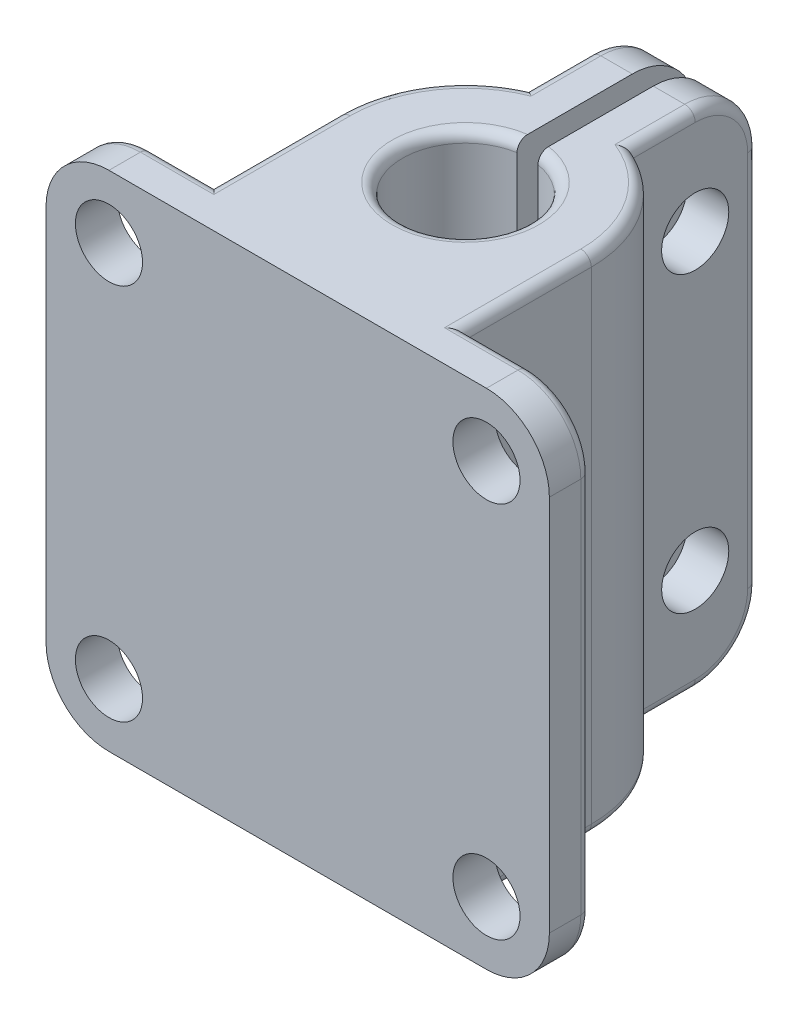
SolidWorks part; units mm, degrees
ref_plane "Front Plane" through (0, 0, 0) normal (0, 0, 1) x (1, 0, 0)
ref_plane "Top Plane" through (0, 0, 0) normal (0, 1, 0) x (1, 0, 0)
ref_plane "Right Plane" through (0, 0, 0) normal (1, 0, 0) x (0, 0, -1)
sketch "Sketch1" plane through (0, 0, 0) normal (0, 1, 0) x (1, 0, 0)
  line L21 (-6, 6) -> (-6, 0)
  line L22 (-6, 0) -> (6, 0)
  line L23 (0, -6.3325) -> (0, 25.8956) construction
  line L24 (-2.5, 11.4544) -> (-2.5, 17.4544)
  line L25 (-2.5, 17.4544) -> (-0.5, 17.4544)
  line L26 (-0.5, 17.4544) -> (-0.5, 8.958)
  line L27 (6, 6) -> (6, 0)
  line L28 (2.5, 11.4544) -> (2.5, 17.4544)
  line L29 (2.5, 17.4544) -> (0.5, 17.4544)
  line L30 (0.5, 17.4544) -> (0.5, 8.958)
  circle A4 centre (0, 6) radius 3 construction
  circle A5 centre (0, 6) radius 6 construction
  arc A6 (-6, 6) -> (-2.5, 11.4544) centre (0, 6) cw
  arc A7 (-0.5, 8.958) -> (0.5, 8.958) centre (0, 6) ccw
  arc A8 (6, 6) -> (2.5, 11.4544) centre (0, 6) ccw
  point P13 (0, 0)
  dimension "D2" = 12
  dimension "D1" = 6
  dimension "D3" = 2
  dimension "D4" = 0.5
  dimension "D5" = 6
extrude "Boss-Extrude1" add sketch "Sketch1" along normal blind 24
sketch "Sketch2" plane through (2.5, 0, 0) normal (1, 0, 0) x (0, 0, -1)
  line L0 (11.4544, 24) -> (17.4544, 24) construction
  line L1 (17.4544, 12) -> (0, 12) construction
  line L3 (17.4544, 24) -> (17.4544, 0) construction
  line L4 (0, 24) -> (0, 0) construction
  circle A0 centre (14.4544, 19) radius 1.6
  circle A1 centre (14.4544, 5) radius 1.6
  point P5 (14.4544, 24)
  dimension "D2" = 3.2
  dimension "D1" = 5
extrude "Cut-Extrude1" cut sketch "Sketch2" against normal through all
sketch "Sketch3" plane through (0, 0, 0) normal (0, 0, 1) x (1, 0, 0)
  line L0 (-6, 24) -> (6, 24) construction
  line L1 (12, 0) -> (-12, 0)
  line L2 (12, 0) -> (12, 24)
  line L3 (12, 24) -> (-12, 24)
  line L4 (-12, 0) -> (-12, 24)
  line L5 (-6, 0) -> (6, 0) construction
  line L6 (6, 24) -> (6, 0) construction
  point P8 (0, 24)
  dimension "D1" = 6
extrude "Boss-Extrude2" add sketch "Sketch3" along normal blind 2
sketch "Sketch4" plane through (0, 0, 0) normal (0, 0, -1) x (-1, 0, 0)
  line L0 (12, 12) -> (-12, 12) construction
  line L1 (12, 24) -> (12, 0) construction
  line L2 (-12, 0) -> (-12, 24) construction
  line L3 (12, 0) -> (6, 0) construction
  line L4 (0, 0) -> (0, 24) construction
  line L5 (3, 24) -> (-3, 24) construction
  circle A0 centre (9, 3) radius 1.6
  circle A1 centre (9, 21) radius 1.6
  circle A2 centre (-9, 21) radius 1.6
  circle A3 centre (-9, 3) radius 1.6
  point P18 (9, 0)
  dimension "D1" = 3.2
  dimension "D2" = 3
extrude "Cut-Extrude2" cut sketch "Sketch4" against normal blind 3
fillet "Fillet3" radius 3 4 edges at (-12, 0, 1) (12, 0, 1) (12, 24, 1) (-12, 24, 1)
fillet "Fillet4" radius 3 4 edges at (1.5, 0, -17.4544) (1.5, 24, -17.4544) (-1.5, 0, -17.4544) (-1.5, 24, -17.4544)
fillet "Fillet5" radius 0.5 2 edges at (0, 24, -3) (0, 0, -3)
fillet "Fillet6" radius 0.5 28 edges at (7.5, 0, 0) (11.1213, 0.8787, 0) (7.5, 24, 0) (11.1213, 23.1213, 0) (-7.5, 0, 0) (-11.1213, 0.8787, 0) (-12, 12, 0) (-7.5, 24, 0) (-2.5, 0, -12.9544) (-2.5, 0.8787, -16.5757) (-2.5, 12, -17.4544) (-2.5, 23.1213, -16.5757) (2.5, 0, -12.9544) (2.5, 0.8787, -16.5757) (2.5, 12, -17.4544) (2.5, 23.1213, -16.5757) (-6, 0, -3) (6, 0, -3) (-6, 24, -3) (6, 24, -3) (12, 12, 0) (-11.1213, 23.1213, 0) (-2.5, 24, -12.9544) (2.5, 24, -12.9544) (-5.0498, 0, -9.2404) (5.0498, 0, -9.2404) (-5.0498, 24, -9.2404) (5.0498, 24, -9.2404)
